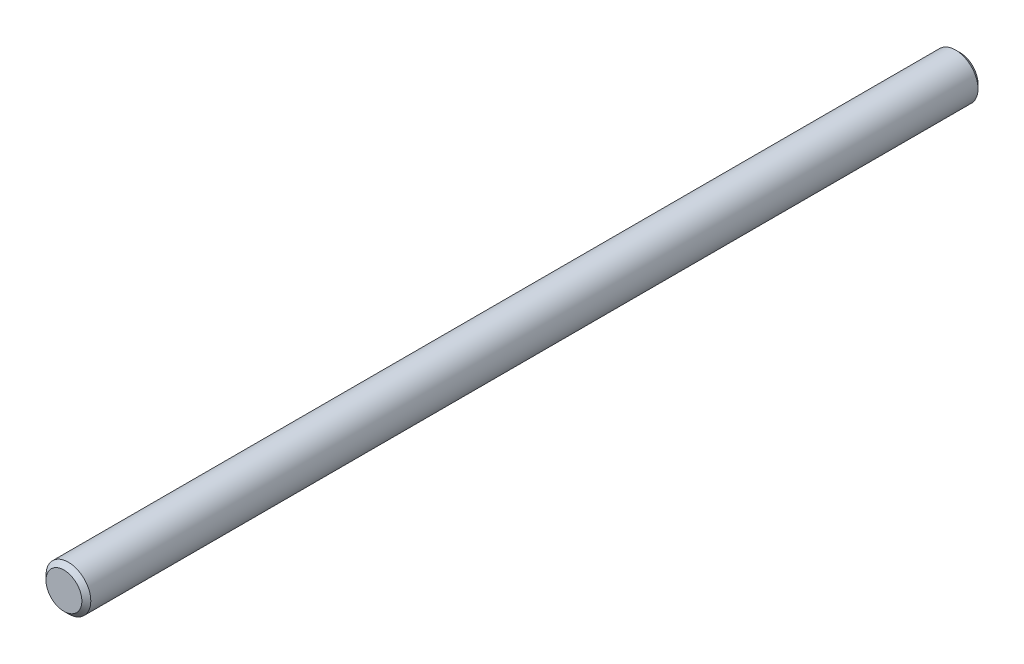
SolidWorks part; units mm, degrees
ref_plane "Front" through (0, 0, 0) normal (0, 0, 1) x (1, 0, 0)
ref_plane "Top" through (0, 0, 0) normal (0, 1, 0) x (1, 0, 0)
ref_plane "Right" through (0, 0, 0) normal (1, 0, 0) x (0, 0, -1)
sketch "Sketch1" plane through (0, 0, 0) normal (0, 0, 1) x (1, 0, 0)
  circle A0 centre (0, 0) radius 5
  dimension "dia" = 10
extrude "Extrude1" add sketch "Sketch1" along normal mid plane 200
sketch "Sketch2" plane through (0, 0, 0) normal (1, 0, 0) x (0, 0, -1)
  line L0 (100, 5) -> (-100, 5) construction
  point P0 (-100, 5)
  point P1 (100, 5)
  point P2 (-80, 5)
  point P5 (80, 5)
  dimension "D1" = 20
  dimension "D2" = 20
chamfer "Chamfer1" distance 1 angle 45 2 edges at (5, 0, -100) (5, 0, 100)
equation "\"D1@Chamfer1\" = \"dia@Sketch1\" * .1"
equation "\"D1@Sketch2\"=\"dia@sketch1\"*2"
equation "\"D2@Sketch2\"=\"D1@Sketch2\""
